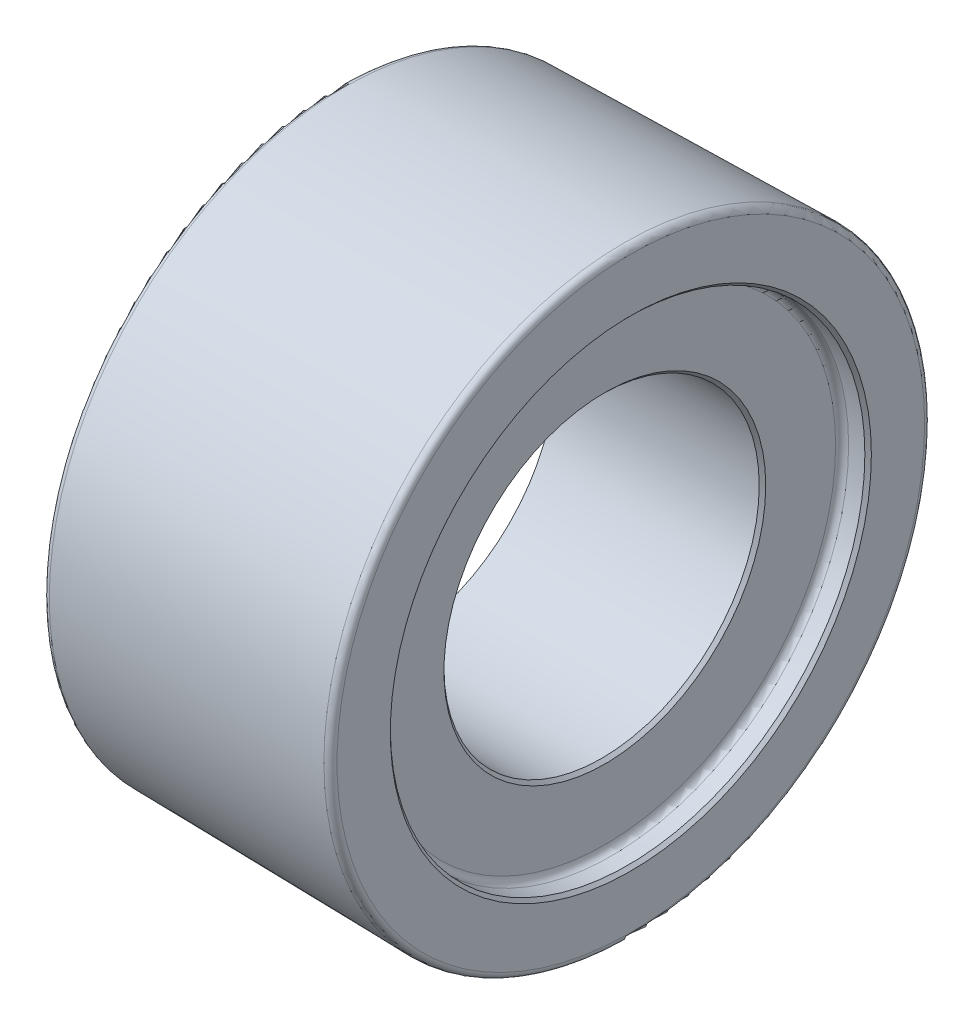
SolidWorks part; units mm, degrees
ref_plane "Ebene vorne" through (0, 0, 0) normal (0, 0, 1) x (1, 0, 0)
ref_plane "Ebene oben" through (0, 0, 0) normal (0, 1, 0) x (1, 0, 0)
ref_plane "Ebene rechts" through (0, 0, 0) normal (1, 0, 0) x (0, 0, -1)
sketch "Skizze1" plane through (0, 0, 0) normal (0, 0, 1) x (1, 0, 0)
  line L0 (0, 0) -> (74.9348, 0) construction
  line L1 (0, -40.15) -> (0, -45.4245)
  line L2 (0, -45.4245) -> (45, -46.21)
  line L3 (45, -46.21) -> (45, -36.5)
  line L4 (45, -36.5) -> (41, -36.5)
  line L5 (41, -36.5) -> (41, -24.25)
  line L6 (41, -24.25) -> (9.1799, -24.25)
  line L7 (9.1799, -24.25) -> (0, -40.15)
  line L8 (45, -46.21) -> (28.4559, -46.21) construction
  dimension "D1" = 73
  dimension "D2" = 48.5
  dimension "D3" = 45
  dimension "D4" = 4
  dimension "D5" = 80.3
  dimension "D6" = 1
  dimension "D7" = 60
  dimension "D8" = 92.42
  dimension "D9" = 90.849
revolve "Rotation1" add sketch "Skizze1" angle 360 about L0
fillet "Verrundung1" radius 1 2 edges at (45, 0, 46.21) (0, 0, 45.4245)
chamfer "Fase1" distance 0.5 angle 45 2 edges at (41, 0, 24.25) (45, 0, 36.5)
fillet "Verrundung2" radius 1 1 edges at (41, 0, 36.5)
